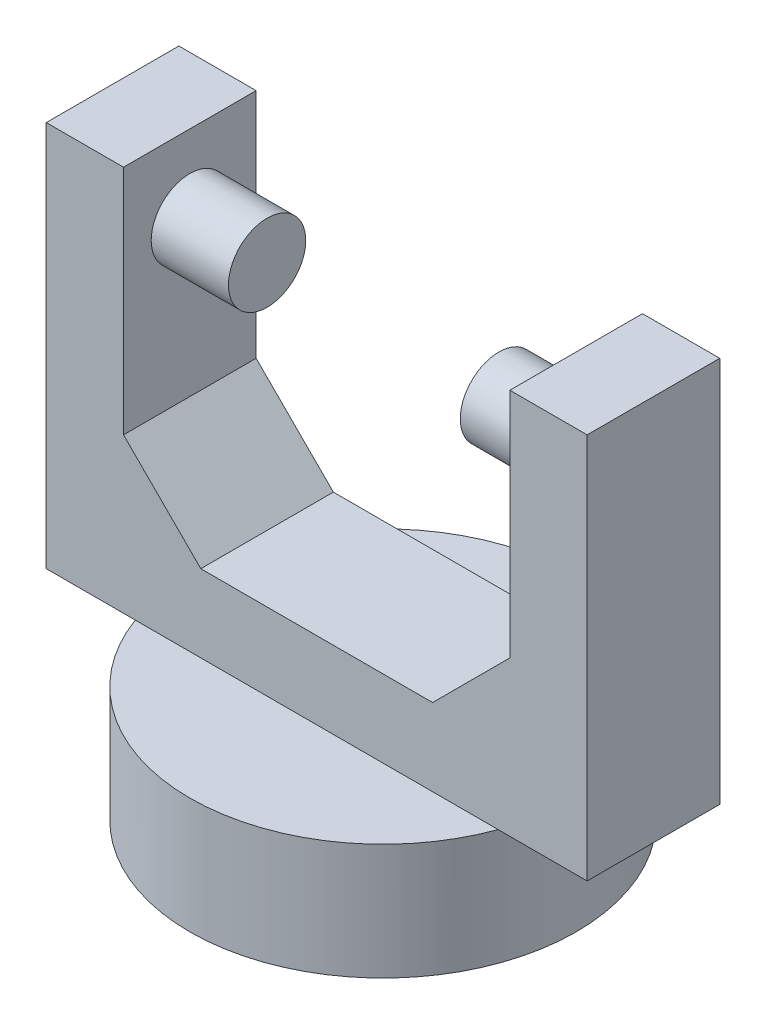
SolidWorks part; units mm, degrees
ref_plane "Front Plane" through (0, 0, 0) normal (0, 0, 1) x (1, 0, 0)
ref_plane "Top Plane" through (0, 0, 0) normal (0, 1, 0) x (1, 0, 0)
ref_plane "Right Plane" through (0, 0, 0) normal (1, 0, 0) x (0, 0, -1)
sketch "Sketch1" plane through (0, 0, 0) normal (0, 1, 0) x (1, 0, 0)
  circle A0 centre (0, 0) radius 12.5
  dimension "D1" = 25
extrude "Boss-Extrude1" add sketch "Sketch1" along normal blind 7.5
sketch "Sketch2" plane through (0, 7.5, 0) normal (0, 1, 0) x (1, 0, 0)
  line L1 (-17.5, 4.2904) -> (17.5, 4.2904)
  line L2 (-17.5, 4.2904) -> (-17.5, -4.2904)
  line L3 (-17.5, -4.2904) -> (17.5, -4.2904)
  line L4 (17.5, 4.2904) -> (17.5, -4.2904)
  point P4 (17.5, 0)
  point P6 (0, 4.2904)
  dimension "D1" = 35
  dimension "D3" = 8.5808
extrude "Boss-Extrude2" add sketch "Sketch2" along normal blind 25
sketch "Sketch3" plane through (0, 32.5, 0) normal (0, 1, 0) x (1, 0, 0)
  line L0 (17.5, 4.2904) -> (-17.5, 4.2904) construction
  line L1 (-12.5, 4.2904) -> (12.5, 4.2904)
  line L2 (-12.5, 4.2904) -> (-12.5, -4.2904)
  line L3 (-12.5, -4.2904) -> (12.5, -4.2904)
  line L4 (12.5, 4.2904) -> (12.5, -4.2904)
  line L5 (-17.5, -4.2904) -> (17.5, -4.2904) construction
  line L6 (17.5, -4.2904) -> (17.5, 4.2904) construction
  line L7 (-17.5, 4.2904) -> (-17.5, -4.2904) construction
  dimension "D1" = 5
  dimension "D2" = 5
extrude "Cut-Extrude1" cut sketch "Sketch3" against normal blind 20
sketch "Sketch4" plane through (-12.5, 0, 0) normal (1, 0, 0) x (0, 0, -1)
  line L0 (4.2904, 12.5) -> (-4.2904, 12.5) construction
  line L1 (4.2904, 32.5) -> (-4.2904, 32.5) construction
  circle A0 centre (0, 27.5) radius 2.5
  point P8 (0, 32.5)
  dimension "D1" = 5
  dimension "D2" = 15
extrude "Boss-Extrude3" add sketch "Sketch4" along normal blind 5
sketch "Sketch5" plane through (12.5, 0, 0) normal (-1, 0, 0) x (0, 0, 1)
  circle A0 centre (0, 27.5) radius 2.5
  circle A1 centre (0, 27.5) radius 2.5 construction
  dimension "D1" = 5
extrude "Boss-Extrude4" add sketch "Sketch5" along normal blind 5
chamfer "Chamfer1" distance 5 angle 45 1 edges at (-12.5, 12.5, 0)
chamfer "Chamfer2" distance 5 angle 45 1 edges at (12.5, 12.5, 0)
